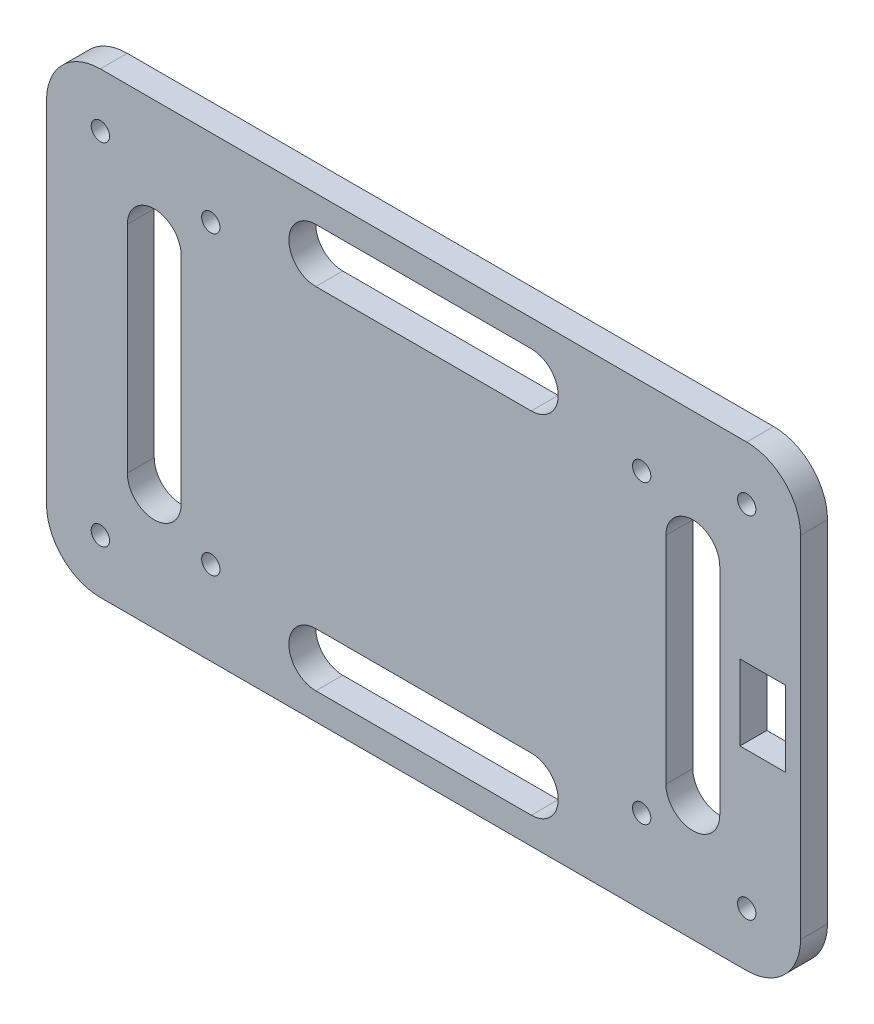
SolidWorks part; units mm, degrees
ref_plane "Front Plane" through (0, 0, 0) normal (0, 0, 1) x (1, 0, 0)
ref_plane "Top Plane" through (0, 0, 0) normal (0, 1, 0) x (1, 0, 0)
ref_plane "Right Plane" through (0, 0, 0) normal (1, 0, 0) x (0, 0, -1)
sketch "Sketch1" plane through (0, 0, 0) normal (0, 0, 1) x (1, 0, 0)
  line L1 (-60, -42.5) -> (60, -42.5)
  line L2 (-70, -32.5) -> (-70, 32.5)
  line L3 (-60, 42.5) -> (60, 42.5)
  line L4 (70, -32.5) -> (70, 32.5)
  line L5 (-70, -42.5) -> (70, 42.5) construction
  line L6 (-70, 42.5) -> (70, -42.5) construction
  arc A0 (-70, 32.5) -> (-60, 42.5) centre (-60, 32.5) cw
  arc A1 (70, 32.5) -> (60, 42.5) centre (60, 32.5) ccw
  arc A2 (-70, -32.5) -> (-60, -42.5) centre (-60, -32.5) ccw
  arc A3 (60, -42.5) -> (70, -32.5) centre (60, -32.5) ccw
  point P0 (0, 0)
  dimension "D3" = 10
  dimension "D4" = 10
  dimension "D5" = 10
  dimension "D6" = 10
  dimension "D1" = 140
  dimension "D2" = 85
extrude "Boss-Extrude1" add sketch "Sketch1" along normal blind 5
sketch "Sketch2" plane through (0, 0, 0) normal (0, 0, 1) x (1, 0, 0)
  line L0 (-39.5, 28.1) -> (-39.5, -26.9) construction
  line L1 (-44.5, 32.5) -> (44.5, 32.5)
  line L2 (-44.5, 32.5) -> (-44.5, -32.5)
  line L3 (-44.5, -32.5) -> (44.5, -32.5)
  line L4 (44.5, 32.5) -> (44.5, -32.5)
  line L5 (-44.5, 32.5) -> (44.5, -32.5) construction
  line L6 (-44.5, -32.5) -> (44.5, 32.5) construction
  line L7 (-44.5, 32.5) -> (-39.5, 32.5)
  line L8 (-44.5, 32.5) -> (-44.5, 28.1)
  line L9 (-44.5, 28.1) -> (-39.5, 28.1)
  line L10 (-39.5, 32.5) -> (-39.5, 28.1)
  line L11 (44.5, 32.5) -> (38.4754, 32.5)
  line L12 (44.5, 32.5) -> (44.5, 28.1)
  line L15 (44.5, 32.5) -> (39.5, 32.5)
  line L16 (44.5, 32.5) -> (44.5, 28.8483)
  line L19 (-39.5, -26.9) -> (40.5, -26.9) construction
  line L20 (40.5, -26.9) -> (40.5, 28.1) construction
  line L21 (0, 42.5) -> (0, 32.5) construction
  line L23 (60, 42.5) -> (-60, 42.5) construction
  line L24 (-20, 32.5) -> (20, 32.5) construction
  line L25 (0, -42.5) -> (0, -32.5) construction
  line L26 (-20, 37.5) -> (20, 37.5)
  line L27 (-20, 27.5) -> (20, 27.5)
  line L28 (-60, -42.5) -> (60, -42.5) construction
  line L29 (-20, -32.5) -> (20, -32.5) construction
  line L30 (-70, 0) -> (-50, 0) construction
  line L31 (-20, -27.5) -> (20, -27.5)
  line L32 (-20, -37.5) -> (20, -37.5)
  line L33 (-70, 32.5) -> (-60, 32.5)
  line L34 (-70, 32.5) -> (-70, 42.5)
  line L35 (-70, 42.5) -> (-60, 42.5)
  line L36 (-60, 32.5) -> (-60, 42.5)
  line L37 (70, 32.5) -> (60, 32.5)
  line L38 (70, 32.5) -> (70, 42.5)
  line L39 (70, 42.5) -> (60, 42.5)
  line L40 (60, 32.5) -> (60, 42.5)
  line L41 (70, -32.5) -> (60, -32.5)
  line L42 (70, -32.5) -> (70, -42.5)
  line L43 (70, -42.5) -> (60, -42.5)
  line L44 (60, -32.5) -> (60, -42.5)
  line L45 (-70, -32.5) -> (-60, -32.5)
  line L46 (-70, -32.5) -> (-70, -42.5)
  line L47 (-70, -42.5) -> (-60, -42.5)
  line L48 (-60, -32.5) -> (-60, -42.5)
  line L49 (-70, 32.5) -> (-70, -32.5) construction
  line L50 (70, 0) -> (50, 0) construction
  line L51 (70, -32.5) -> (70, 32.5) construction
  line L52 (-50, 20) -> (-50, -20) construction
  line L53 (58.7458, 7) -> (67.2458, 7)
  line L54 (-45, 20) -> (-45, -20)
  line L55 (-55, 20) -> (-55, -20)
  line L56 (50, 20) -> (50, -20) construction
  line L57 (55, 20) -> (55, -20)
  line L58 (45, 20) -> (45, -20)
  line L59 (58.7458, 7) -> (58.7458, -7)
  line L60 (58.7458, -7) -> (67.2458, -7)
  line L61 (67.2458, 7) -> (67.2458, -7)
  line L62 (58.7458, 7) -> (67.2458, -7) construction
  line L63 (58.7458, -7) -> (67.2458, 7) construction
  circle A0 centre (-39.5, 28.1) radius 1.7
  circle A3 centre (-39.5, -26.9) radius 1.7
  circle A4 centre (40.5, -26.9) radius 1.7
  circle A5 centre (40.5, 28.1) radius 1.7
  arc A6 (-20, 37.5) -> (-20, 27.5) centre (-20, 32.5) ccw
  arc A7 (20, 27.5) -> (20, 37.5) centre (20, 32.5) ccw
  arc A8 (-20, -27.5) -> (-20, -37.5) centre (-20, -32.5) ccw
  arc A9 (20, -37.5) -> (20, -27.5) centre (20, -32.5) ccw
  arc A10 (60, -42.5) -> (70, -32.5) centre (60, -32.5) ccw construction
  circle A11 centre (-60, 32.5) radius 1.7
  circle A12 centre (-60, -32.5) radius 1.7
  circle A13 centre (60, -32.5) radius 1.7
  circle A14 centre (60, 32.5) radius 1.7
  arc A15 (-45, 20) -> (-55, 20) centre (-50, 20) ccw
  arc A16 (-55, -20) -> (-45, -20) centre (-50, -20) ccw
  arc A17 (55, 20) -> (45, 20) centre (50, 20) ccw
  arc A18 (45, -20) -> (55, -20) centre (50, -20) ccw
  point P0 (0, 0)
  point P28 (0, 32.5)
  point P39 (0, -32.5)
  point P83 (62.9958, 0)
  point P84 (-50, 0)
  point P90 (50, 0)
  dimension "D1" = 4.4
  dimension "D2" = 5
  dimension "D3" = 89
  dimension "D4" = 65
extrude "Cut-Extrude9" cut sketch "Sketch2" along normal blind 5 contours L27 A7 L1 A6 | L1 A7 L26 A6 | L58 A18 L57 A17 | L40 A14 L37 | L37 A14 L40 | L41 A13 L44 | L44 A13 L41 | A4 | L3 A9 L31 A8 | L32 A9 L3 A8 | A3 | L10 A0 L9 | L9 A0 L10 | L55 A16 L54 A15 | L33 A11 L36 | L36 A11 L33 | L45 A12 L48 | L48 A12 L45 | A5 | L59 L53 L61 L60
